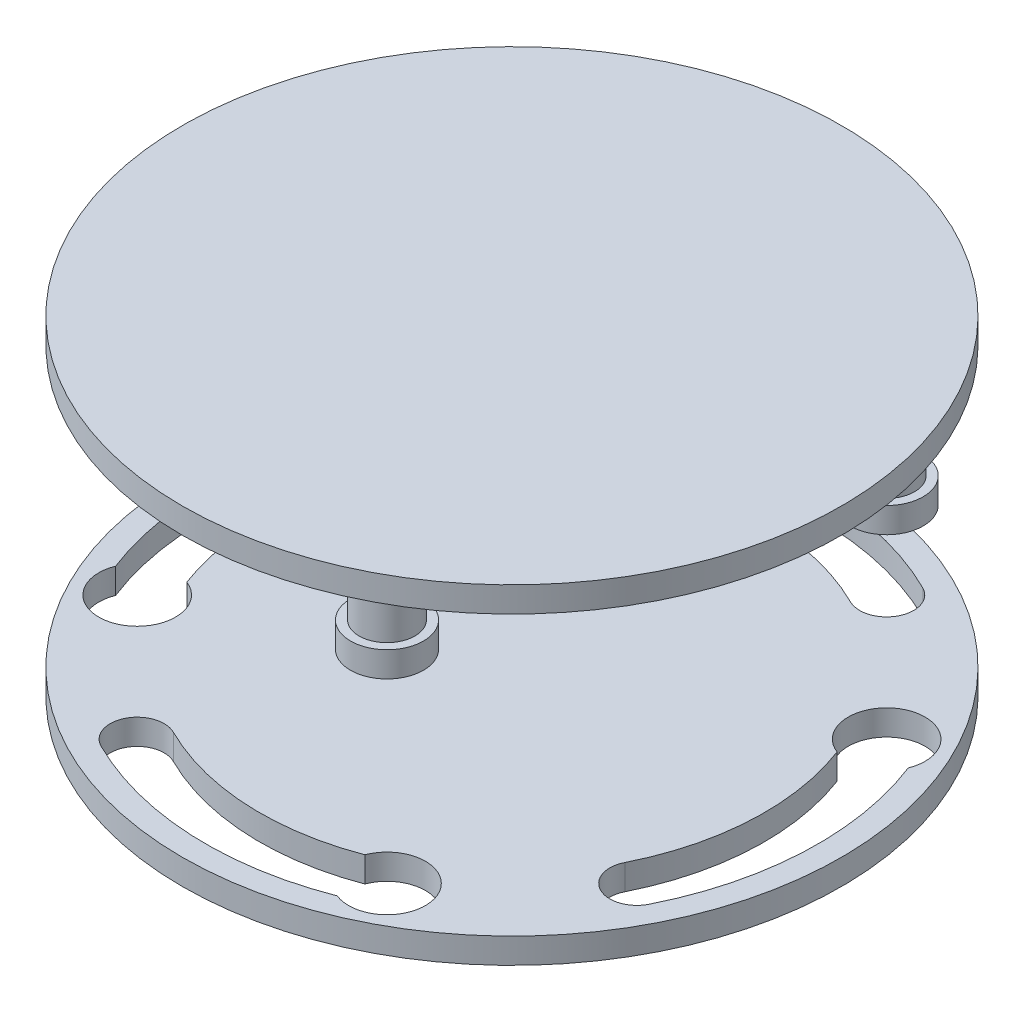
SolidWorks part; units mm, degrees
ref_plane "Front Plane" through (0, 0, 0) normal (0, 0, 1) x (1, 0, 0)
ref_plane "Top Plane" through (0, 0, 0) normal (0, 1, 0) x (1, 0, 0)
ref_plane "Right Plane" through (0, 0, 0) normal (1, 0, 0) x (0, 0, -1)
sketch "Sketch1" plane through (0, 0, 0) normal (0, 1, 0) x (1, 0, 0)
  circle A0 centre (0, 0) radius 65
extrude "Boss-Extrude1" add sketch "Sketch1" along normal blind 5
sketch "Sketch2" plane through (0, 5, 0) normal (0, 1, 0) x (1, 0, 0)
  line L0 (0, 65) -> (0, -65) construction
  line L1 (-65, 0) -> (65, 0)
  line L2 (65, 0) -> (65, -65)
  line L3 (65, -65) -> (0, -65)
  line L4 (0, -65) -> (-65, -65)
  line L5 (-65, -65) -> (-65, 0)
  line L6 (-65, 0) -> (-65, 65) construction
  line L7 (-65, 65) -> (65, 65) construction
  line L8 (65, 65) -> (65, 0) construction
  line L9 (-65, 65) -> (65, -65) construction
  line L10 (65, 65) -> (-65, -65) construction
  line L11 (-65, 32.5) -> (0, 0) construction
  line L12 (0, 0) -> (-65, -32.5) construction
  circle A0 centre (0, 0) radius 65 construction
  arc A1 (-49.2715, -24.6358) -> (-49.2715, 24.6358) centre (0, 0) cw construction
  arc A2 (-54.0282, 27.0141) -> (-56.2894, -21.9159) centre (0, 0) ccw
  arc A3 (-44.5148, 22.2574) -> (-46.5475, -17.6152) centre (0, 0) ccw
  arc A4 (-44.5148, 22.2574) -> (-54.0282, 27.0141) centre (-49.2715, 24.6358) ccw
  arc A5 (49.2715, -24.6358) -> (49.2715, 24.6358) centre (0, 0) ccw construction
  arc A6 (-46.5691, -17.5579) -> (-56.316, -21.8475) centre (-49.2715, -24.6358) cw
  arc A8 (56.2681, 21.9704) -> (56.2894, -21.9159) centre (0, 0) cw
  arc A10 (46.5448, 17.6223) -> (46.5475, -17.6152) centre (0, 0) cw
  arc A11 (22.2574, 44.5148) -> (27.0141, 54.0282) centre (24.6358, 49.2715) ccw
  arc A12 (27.0141, 54.0282) -> (-21.9159, 56.2894) centre (0, 0) ccw
  arc A13 (-24.6358, 49.2715) -> (24.6358, 49.2715) centre (0, 0) cw construction
  arc A14 (-17.5579, 46.5691) -> (-21.8475, 56.316) centre (-24.6358, 49.2715) cw
  arc A15 (22.2574, 44.5148) -> (-17.6152, 46.5475) centre (0, 0) ccw
  arc A16 (-22.2574, -44.5148) -> (-27.0141, -54.0282) centre (-24.6358, -49.2715) ccw
  arc A17 (-22.2574, -44.5148) -> (17.6152, -46.5475) centre (0, 0) ccw
  arc A18 (24.6358, -49.2715) -> (-24.6358, -49.2715) centre (0, 0) cw construction
  arc A19 (-27.0141, -54.0282) -> (21.9159, -56.2894) centre (0, 0) ccw
  arc A20 (17.5579, -46.5691) -> (21.8475, -56.316) centre (24.6358, -49.2715) cw
  arc A21 (46.5691, 17.5579) -> (56.316, 21.8475) centre (49.2715, 24.6358) cw
  arc A22 (44.5148, -22.2574) -> (54.0282, -27.0141) centre (49.2715, -24.6358) ccw
  arc A23 (54.0282, -27.0141) -> (56.2894, 21.9159) centre (0, 0) ccw
  arc A24 (44.5148, -22.2574) -> (46.5475, 17.6152) centre (0, 0) ccw
  point P18 (-55.0872, 0)
extrude "Cut-Extrude2" cut sketch "Sketch2" against normal blind 5
sketch "Sketch6" plane through (0, 5, 0) normal (0, 1, 0) x (1, 0, 0)
  circle A0 centre (0, 0) radius 65
sketch "Sketch8" plane through (0, 0, 0) normal (1, 0, 0) x (0, 0, -1)
  line L0 (0, 0) -> (0, 60) construction
  dimension "D1" = 60
ref_plane "Plane1" through (0, 60, 0) normal (0, 1, 0) x (1, 0, 0)
sketch "Sketch10" plane through (0, 60, 0) normal (0, 1, 0) x (1, 0, 0)
  circle A0 centre (0, 0) radius 65
extrude "Boss-Extrude3" add sketch "Sketch10" along normal blind 5 separate body
sketch "Sketch13" plane through (0, 60, 0) normal (0, 1, 0) x (1, 0, 0)
  circle A0 centre (-24.6379, 49.2957) radius 7.6005
sketch "Sketch14" plane through (0, 60, 0) normal (0, -1, 0) x (1, 0, 0)
  circle A0 centre (-24.6379, -49.2957) radius 5.5
extrude "Boss-Extrude4" add sketch "Sketch14" along normal blind 10
sketch "Sketch18" plane through (0, 50, 0) normal (0, -1, 0) x (1, 0, 0)
  circle A0 centre (-24.6379, -49.2957) radius 7.2
extrude "Boss-Extrude5" add sketch "Sketch18" along normal blind 5
sketch "Sketch21" plane through (0, 60, 0) normal (0, 1, 0) x (1, 0, 0)
  circle A0 centre (-49.2729, -24.6297) radius 5.5
extrude "Boss-Extrude6" add sketch "Sketch21" against normal blind 10
sketch "Sketch25" plane through (0, 50, 0) normal (0, -1, 0) x (1, 0, 0)
  circle A0 centre (-49.2536, 24.6488) radius 7.2
extrude "Boss-Extrude7" add sketch "Sketch25" along normal blind 5
sketch "Sketch27" plane through (0, 60, 0) normal (0, 1, 0) x (1, 0, 0)
  circle A0 centre (49.2715, 24.6358) radius 5.5
  circle A1 centre (24.6358, -49.2715) radius 5.5
extrude "Boss-Extrude9" add sketch "Sketch27" against normal blind 10
sketch "Sketch28" plane through (0, 50, 0) normal (0, -1, 0) x (1, 0, 0)
  circle A0 centre (49.2715, -24.6358) radius 7.2
  circle A1 centre (24.6358, 49.2715) radius 7.2
extrude "Boss-Extrude10" add sketch "Sketch28" along normal blind 5
sketch "Sketch29" plane through (0, 0, 0) normal (0, -1, 0) x (1, 0, 0)
  circle A0 centre (0, 0) radius 4
extrude "Boss-Extrude11" add sketch "Sketch29" along normal blind 5
sketch "Sketch32" plane through (0, -5, 0) normal (0, -1, 0) x (1, 0, 0)
  circle A0 centre (0, 0) radius 1
extrude "Cut-Extrude4" cut sketch "Sketch32" against normal blind 5
